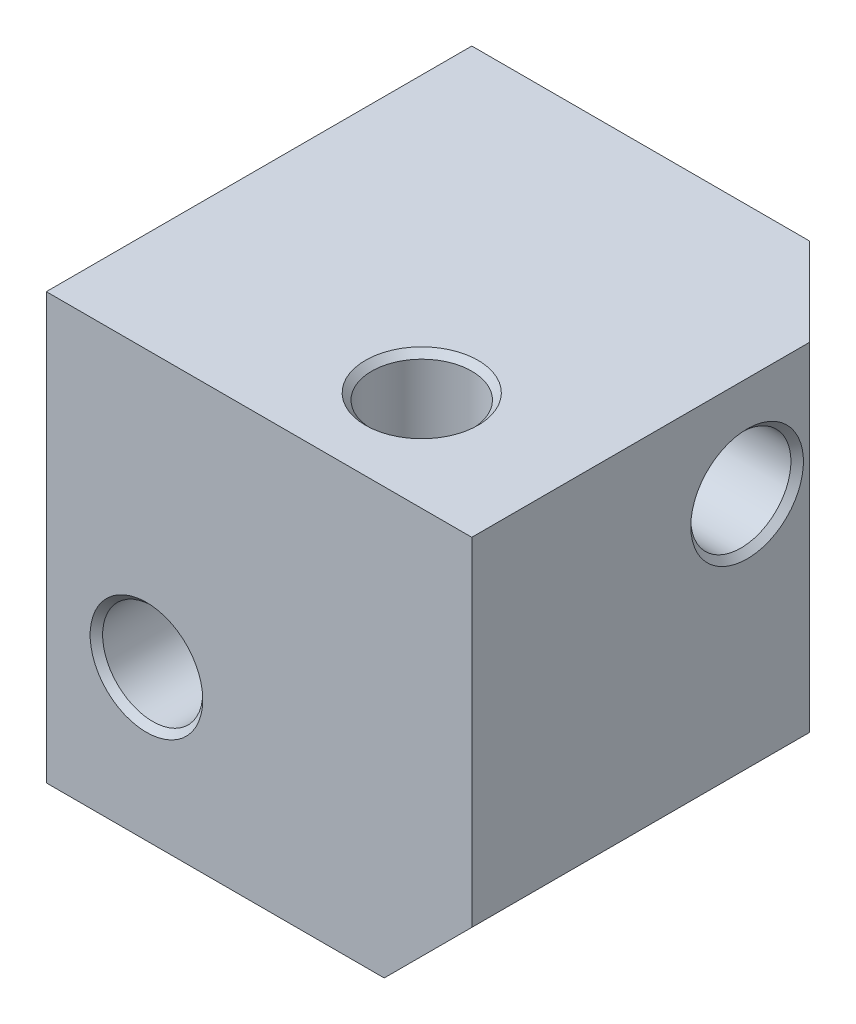
SolidWorks part; units mm, degrees
ref_plane "Спереди" through (0, 0, 0) normal (0, 0, 1) x (1, 0, 0)
ref_plane "Сверху" through (0, 0, 0) normal (0, 1, 0) x (1, 0, 0)
ref_plane "Справа" through (0, 0, 0) normal (1, 0, 0) x (0, 0, -1)
sketch "Эскиз1" plane through (0, 0, 0) normal (0, 0, 1) x (1, 0, 0)
  line L1 (0, 0) -> (17, 0)
  line L2 (0, 0) -> (0, 17)
  line L3 (0, 17) -> (17, 17)
  line L4 (17, 0) -> (17, 17)
  dimension "D1" = 17
  dimension "D2" = 17
extrude "Бобышка-Вытянуть1" add sketch "Эскиз1" along normal blind 17
hole_wizard "Отверстие обработанное метчиком M4x0.71" positions "Трехмерный эскиз1" profile "Эскиз2" tap size "M4x0.7" standard "Ansi (метрические)" end condition through all
sketch3d "Трехмерный эскиз1"
  line L0 (17, 17, 17) -> (0, 17, 17) construction
  line L1 (0, 17, 17) -> (0, 17, 0) construction
  line L2 (0, 17, 17) -> (0, 0, 17) construction
  point P0 (11, 17, 13)
  point P2 (4, 6, 17)
  point P4 (0, 13, 6)
  dimension "D1" = 4
  dimension "D2" = 11
  dimension "D3" = 4
  dimension "D4" = 11
  dimension "D5" = 4
  dimension "D6" = 11
sketch "Эскиз2" plane through (11, 17, 13) normal (1, 0, 0) x (0, 0, 1)
  line L0 (0, 0) -> (0, 17)
  line L1 (0, 17) -> (2.25, 17)
  line L2 (2, 16.75) -> (2, 0.25)
  line L3 (2, 0.25) -> (2.25, 0)
  line L5 (2.25, 0) -> (0, 0)
  line L6 (-2, 0.25) -> (-2.25, 0) construction
  line L7 (2.25, 17) -> (2, 16.75)
  line L8 (-2.25, 17) -> (-2, 16.75) construction
  line L11 (0, -6.35) -> (0, 107.95) construction
  dimension "Диаметр резьбы" = 4
  dimension "Глубина проходного сверла" = 17
  dimension "Диаметр передней зенковки" = 4.5
  dimension "Угол передней зенковки" = 90
  dimension "Диаметр задней зенковки" = 4.5
  dimension "Угол задней зенковки" = 90
chamfer "Фаска1" distance 3.5 angle 45 3 edges at (17, 8.5, 0) (17, 0, 8.5) (8.5, 0, 0)
